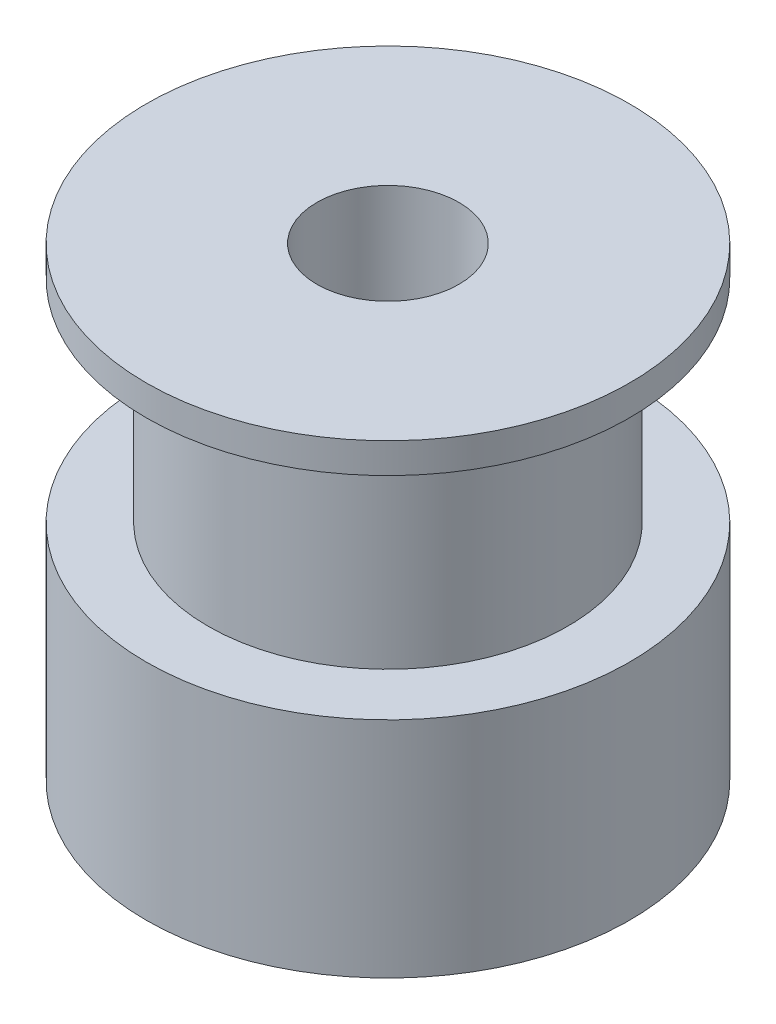
SolidWorks part; units mm, degrees
ref_plane "Front Plane" through (0, 0, 0) normal (0, 0, 1) x (1, 0, 0)
ref_plane "Top Plane" through (0, 0, 0) normal (0, 1, 0) x (1, 0, 0)
ref_plane "Right Plane" through (0, 0, 0) normal (1, 0, 0) x (0, 0, -1)
sketch "Sketch1" plane through (0, 0, 0) normal (0, 1, 0) x (1, 0, 0)
  circle A0 centre (0, 0) radius 8
  dimension "D1" = 16
extrude "Boss-Extrude1" add sketch "Sketch1" along normal blind 7.4
sketch "Sketch2" plane through (0, 7.4, 0) normal (0, 1, 0) x (1, 0, 0)
  circle A0 centre (0, 0) radius 5.95
  dimension "D1" = 11.9
extrude "Boss-Extrude2" add sketch "Sketch2" along normal blind 7
sketch "Sketch3" plane through (0, 14.4, 0) normal (0, 1, 0) x (1, 0, 0)
  circle A1 centre (0, 0) radius 8
  circle A2 centre (0, 0) radius 8
  dimension "D1" = 0
extrude "Boss-Extrude3" add sketch "Sketch3" along normal blind 1
sketch "Sketch4" plane through (0, 0, 0) normal (0, -1, 0) x (1, 0, 0)
  circle A0 centre (0, 0) radius 2.35
  dimension "D1" = 4.7
extrude "Cut-Extrude1" cut sketch "Sketch4" against normal blind 21
